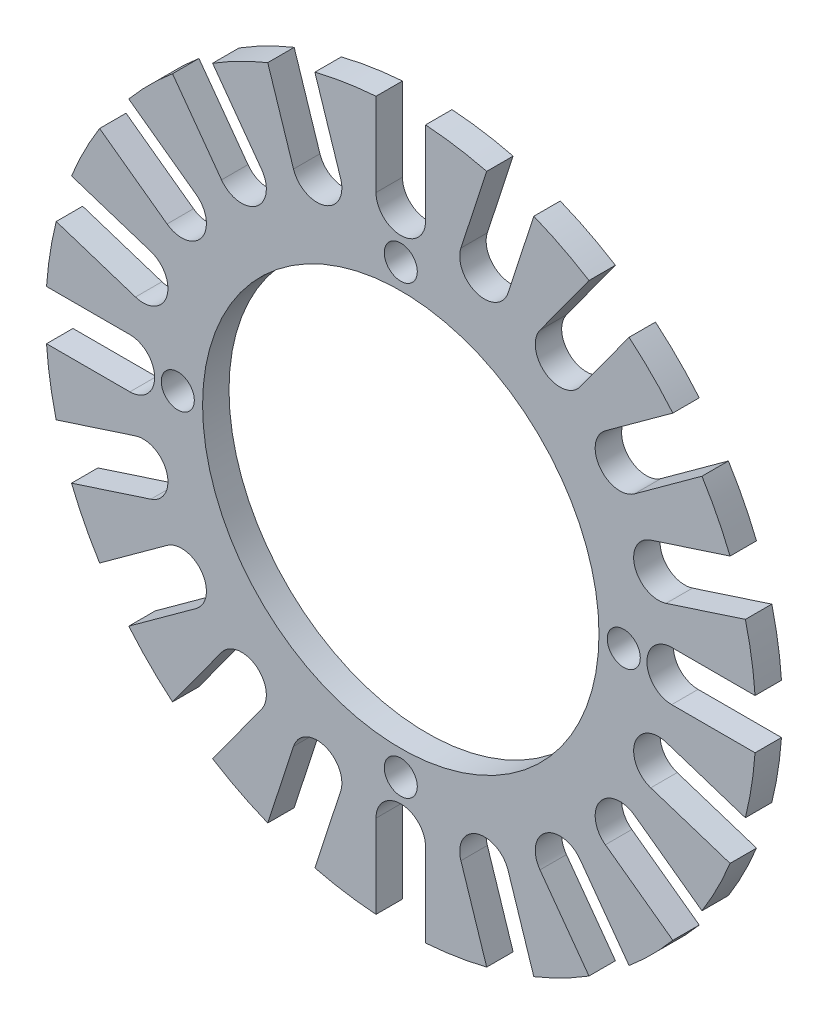
SolidWorks part; units mm, degrees
ref_plane "Front" through (0, 0, 0) normal (0, 0, 1) x (1, 0, 0)
ref_plane "Top" through (0, 0, 0) normal (0, 1, 0) x (1, 0, 0)
ref_plane "Right" through (0, 0, 0) normal (1, 0, 0) x (0, 0, -1)
sketch "Sketch1" plane through (0, 0, 0) normal (0, 0, 1) x (1, 0, 0)
  line L2 (-1.5, 16.4) -> (-1.5, 21.4476)
  line L5 (1.5, 21.4476) -> (1.5, 16.4)
  line L6 (8.0543, 19.9344) -> (6.4945, 15.1338)
  line L7 (3.6413, 16.0609) -> (5.2011, 20.8614)
  line L8 (13.8201, 16.4698) -> (10.8532, 12.3862)
  line L9 (8.4262, 14.1496) -> (11.3931, 18.2332)
  line L10 (18.2332, 11.3931) -> (14.1496, 8.4262)
  line L11 (12.3862, 10.8532) -> (16.4698, 13.8201)
  line L12 (20.8614, 5.2011) -> (16.0609, 3.6413)
  line L13 (15.1338, 6.4945) -> (19.9344, 8.0543)
  line L14 (21.4476, -1.5) -> (16.4, -1.5)
  line L15 (16.4, 1.5) -> (21.4476, 1.5)
  line L16 (19.9344, -8.0543) -> (15.1338, -6.4945)
  line L17 (16.0609, -3.6413) -> (20.8614, -5.2011)
  line L18 (16.4698, -13.8201) -> (12.3862, -10.8532)
  line L19 (14.1496, -8.4262) -> (18.2332, -11.3931)
  line L20 (11.3931, -18.2332) -> (8.4262, -14.1496)
  line L21 (10.8532, -12.3862) -> (13.8201, -16.4698)
  line L22 (5.2011, -20.8614) -> (3.6413, -16.0609)
  line L23 (6.4945, -15.1338) -> (8.0543, -19.9344)
  line L24 (-1.5, -21.4476) -> (-1.5, -16.4)
  line L25 (1.5, -16.4) -> (1.5, -21.4476)
  line L26 (-8.0543, -19.9344) -> (-6.4945, -15.1338)
  line L27 (-3.6413, -16.0609) -> (-5.2011, -20.8614)
  line L28 (-13.8201, -16.4698) -> (-10.8532, -12.3862)
  line L29 (-8.4262, -14.1496) -> (-11.3931, -18.2332)
  line L30 (-18.2332, -11.3931) -> (-14.1496, -8.4262)
  line L31 (-12.3862, -10.8532) -> (-16.4698, -13.8201)
  line L32 (-20.8614, -5.2011) -> (-16.0609, -3.6413)
  line L33 (-15.1338, -6.4945) -> (-19.9344, -8.0543)
  line L34 (-21.4476, 1.5) -> (-16.4, 1.5)
  line L35 (-16.4, -1.5) -> (-21.4476, -1.5)
  line L36 (-19.9344, 8.0543) -> (-15.1338, 6.4945)
  line L37 (-16.0609, 3.6413) -> (-20.8614, 5.2011)
  line L38 (-16.4698, 13.8201) -> (-12.3862, 10.8532)
  line L39 (-14.1496, 8.4262) -> (-18.2332, 11.3931)
  line L40 (-11.3931, 18.2332) -> (-8.4262, 14.1496)
  line L41 (-10.8532, 12.3862) -> (-13.8201, 16.4698)
  line L42 (-5.2011, 20.8614) -> (-3.6413, 16.0609)
  line L43 (-6.4945, 15.1338) -> (-8.0543, 19.9344)
  circle A0 centre (0, 0) radius 12
  circle A2 centre (0, 13.5) radius 1
  circle A5 centre (13.5, 0) radius 1
  circle A6 centre (0, -13.5) radius 1
  circle A7 centre (-13.5, 0) radius 1
  arc A11 (-1.5, 16.4) -> (1.5, 16.4) centre (0, 16.4) ccw
  arc A12 (-1.5, 21.4476) -> (-5.2011, 20.8614) centre (0, 0) ccw
  arc A13 (3.6413, 16.0609) -> (6.4945, 15.1338) centre (5.0679, 15.5973) ccw
  arc A14 (8.4262, 14.1496) -> (10.8532, 12.3862) centre (9.6397, 13.2679) ccw
  arc A15 (12.3862, 10.8532) -> (14.1496, 8.4262) centre (13.2679, 9.6397) ccw
  arc A16 (15.1338, 6.4945) -> (16.0609, 3.6413) centre (15.5973, 5.0679) ccw
  arc A17 (16.4, 1.5) -> (16.4, -1.5) centre (16.4, 0) ccw
  arc A18 (16.0609, -3.6413) -> (15.1338, -6.4945) centre (15.5973, -5.0679) ccw
  arc A19 (14.1496, -8.4262) -> (12.3862, -10.8532) centre (13.2679, -9.6397) ccw
  arc A20 (10.8532, -12.3862) -> (8.4262, -14.1496) centre (9.6397, -13.2679) ccw
  arc A21 (6.4945, -15.1338) -> (3.6413, -16.0609) centre (5.0679, -15.5973) ccw
  arc A22 (1.5, -16.4) -> (-1.5, -16.4) centre (0, -16.4) ccw
  arc A23 (-3.6413, -16.0609) -> (-6.4945, -15.1338) centre (-5.0679, -15.5973) ccw
  arc A24 (-8.4262, -14.1496) -> (-10.8532, -12.3862) centre (-9.6397, -13.2679) ccw
  arc A25 (-12.3862, -10.8532) -> (-14.1496, -8.4262) centre (-13.2679, -9.6397) ccw
  arc A26 (-15.1338, -6.4945) -> (-16.0609, -3.6413) centre (-15.5973, -5.0679) ccw
  arc A27 (-16.4, -1.5) -> (-16.4, 1.5) centre (-16.4, 0) ccw
  arc A28 (-16.0609, 3.6413) -> (-15.1338, 6.4945) centre (-15.5973, 5.0679) ccw
  arc A29 (-14.1496, 8.4262) -> (-12.3862, 10.8532) centre (-13.2679, 9.6397) ccw
  arc A30 (-10.8532, 12.3862) -> (-8.4262, 14.1496) centre (-9.6397, 13.2679) ccw
  arc A31 (-6.4945, 15.1338) -> (-3.6413, 16.0609) centre (-5.0679, 15.5973) ccw
  arc A32 (-8.0543, 19.9344) -> (-11.3931, 18.2332) centre (0, 0) ccw
  arc A33 (5.2011, 20.8614) -> (1.5, 21.4476) centre (0, 0) ccw
  arc A34 (11.3931, 18.2332) -> (8.0543, 19.9344) centre (0, 0) ccw
  arc A35 (16.4698, 13.8201) -> (13.8201, 16.4698) centre (0, 0) ccw
  arc A36 (19.9344, 8.0543) -> (18.2332, 11.3931) centre (0, 0) ccw
  arc A37 (21.4476, 1.5) -> (20.8614, 5.2011) centre (0, 0) ccw
  arc A38 (20.8614, -5.2011) -> (21.4476, -1.5) centre (0, 0) ccw
  arc A39 (18.2332, -11.3931) -> (19.9344, -8.0543) centre (0, 0) ccw
  arc A40 (13.8201, -16.4698) -> (16.4698, -13.8201) centre (0, 0) ccw
  arc A41 (8.0543, -19.9344) -> (11.3931, -18.2332) centre (0, 0) ccw
  arc A42 (1.5, -21.4476) -> (5.2011, -20.8614) centre (0, 0) ccw
  arc A43 (-5.2011, -20.8614) -> (-1.5, -21.4476) centre (0, 0) ccw
  arc A44 (-11.3931, -18.2332) -> (-8.0543, -19.9344) centre (0, 0) ccw
  arc A45 (-16.4698, -13.8201) -> (-13.8201, -16.4698) centre (0, 0) ccw
  arc A46 (-19.9344, -8.0543) -> (-18.2332, -11.3931) centre (0, 0) ccw
  arc A47 (-21.4476, -1.5) -> (-20.8614, -5.2011) centre (0, 0) ccw
  arc A48 (-20.8614, 5.2011) -> (-21.4476, 1.5) centre (0, 0) ccw
  arc A49 (-13.8201, 16.4698) -> (-16.4698, 13.8201) centre (0, 0) ccw
  arc A50 (-18.2332, 11.3931) -> (-19.9344, 8.0543) centre (0, 0) ccw
  dimension "D1" = 4
  dimension "D2" = 20
extrude "Boss-Extrude1" add sketch "Sketch1" along normal blind 1.6
